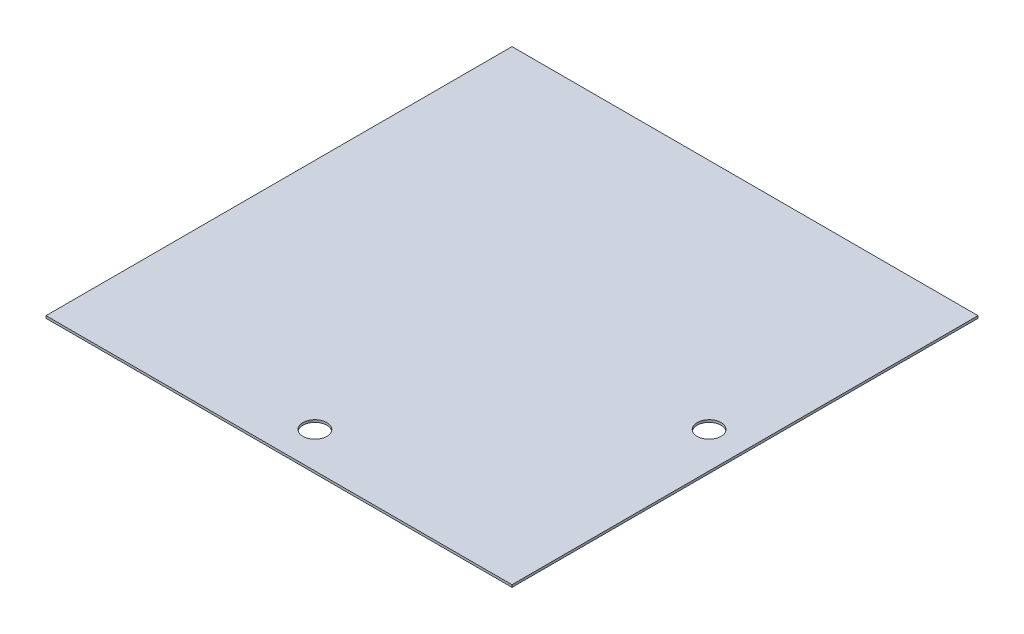
SolidWorks part; units mm, degrees
material "Cedar"
ref_plane "Front Plane" through (0, 0, 0) normal (0, 0, 1) x (1, 0, 0)
ref_plane "Top Plane" through (0, 0, 0) normal (0, 1, 0) x (1, 0, 0)
ref_plane "Right Plane" through (0, 0, 0) normal (1, 0, 0) x (0, 0, -1)
sketch "Sketch1" plane through (0, 0, 0) normal (0, 1, 0) x (1, 0, 0)
  line L1 (-247.4214, -247.4214) -> (247.4214, -247.4214)
  line L2 (-247.4214, -247.4214) -> (-247.4214, 247.4214)
  line L3 (-247.4214, 247.4214) -> (247.4214, 247.4214)
  line L4 (247.4214, -247.4214) -> (247.4214, 247.4214)
  line L5 (-247.4214, -247.4214) -> (247.4214, 247.4214) construction
  line L6 (-247.4214, 247.4214) -> (247.4214, -247.4214) construction
  point P0 (0, 0)
  dimension "D1" = 494.8428
extrude "Boss-Extrude1" add sketch "Sketch1" along normal blind 2.5
sketch "Sketch2" plane through (0, 2.5, 0) normal (0, 1, 0) x (1, 0, 0)
  line L0 (-247.4214, -247.4214) -> (247.4214, -247.4214) construction
  line L1 (247.4214, -247.4214) -> (247.4214, 247.4214) construction
  line L2 (-247.4214, 247.4214) -> (-247.4214, -247.4214) construction
  line L3 (247.4214, 247.4214) -> (-247.4214, 247.4214) construction
  circle A0 centre (209.3214, 0) radius 12.7
  circle A1 centre (0, -209.3214) radius 12.7
  dimension "D1" = 25.4
  dimension "D2" = 25.4
  dimension "D3" = 38.1
  dimension "D4" = 38.1
  dimension "D5" = 247.4214
  dimension "D6" = 247.4214
extrude "Cut-Extrude1" cut sketch "Sketch2" against normal through all
